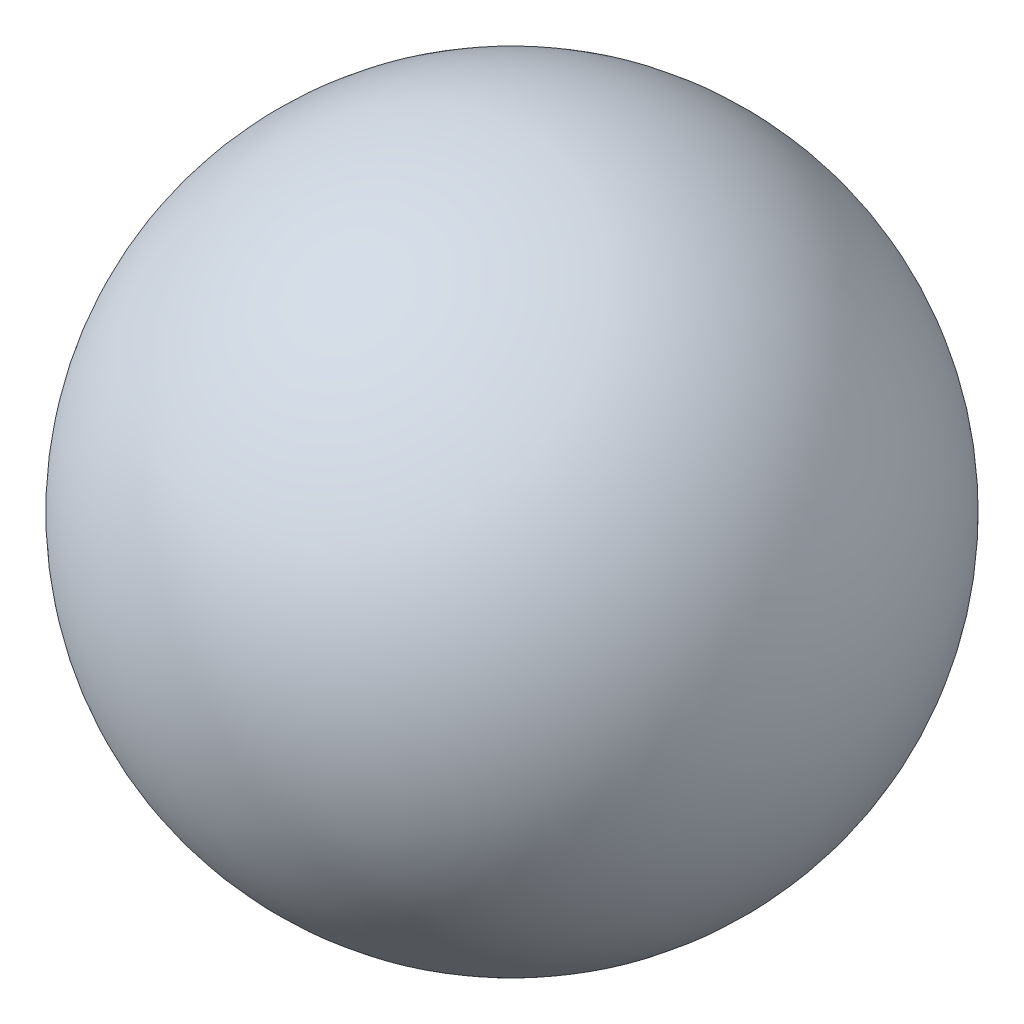
SolidWorks part; units mm, degrees
ref_plane "Front Plane" through (0, 0, 0) normal (0, 0, 1) x (1, 0, 0)
ref_plane "Top Plane" through (0, 0, 0) normal (0, 1, 0) x (1, 0, 0)
ref_plane "Right Plane" through (0, 0, 0) normal (1, 0, 0) x (0, 0, -1)
ref_axis "Axe1" through (0, -24.2, 0) along (0, 1, 0)
sketch "Esquisse2" plane through (0, 0, 0) normal (0, 0, 1) x (1, 0, 0)
  line L0 (0, -22) -> (0, 22)
  line L1 (0, -24.2) -> (0, 24.2) construction
  arc A0 (0, 22) -> (0, -22) centre (0, 0) cw
  point P6 (0, 14.3927)
  point P7 (0, 1.6265)
  point P8 (0, 18.7927)
  point P9 (0, 0)
  point P10 (0, 22)
  dimension "D1" = 22
revolve "Révolution5" add sketch "Esquisse2" angle 360 about axis through (0, -24.2, 0) along (0, 1, 0)
